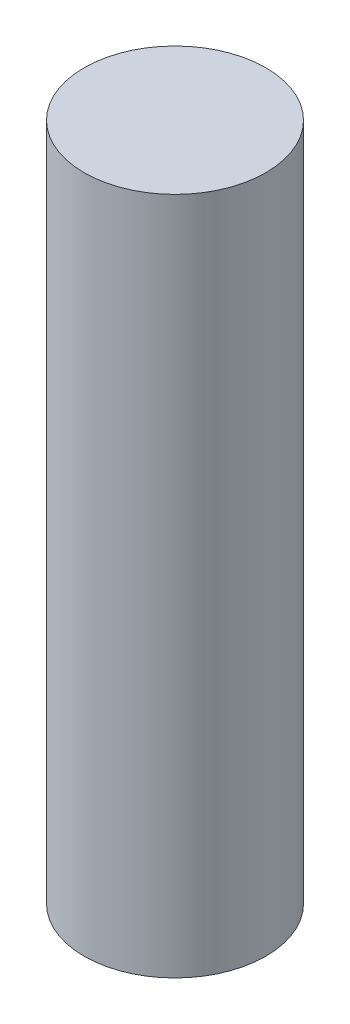
SolidWorks part; units mm, degrees
ref_plane "Front Plane" through (0, 0, 0) normal (0, 0, 1) x (1, 0, 0)
ref_plane "Top Plane" through (0, 0, 0) normal (0, 1, 0) x (1, 0, 0)
ref_plane "Right Plane" through (0, 0, 0) normal (1, 0, 0) x (0, 0, -1)
sketch "Sketch1" plane through (0, 0, 0) normal (0, 1, 0) x (1, 0, 0)
  circle A0 centre (0, 0) radius 3.75
  dimension "D1" = 7.5
extrude "Boss-Extrude1" add sketch "Sketch1" along normal blind 28
